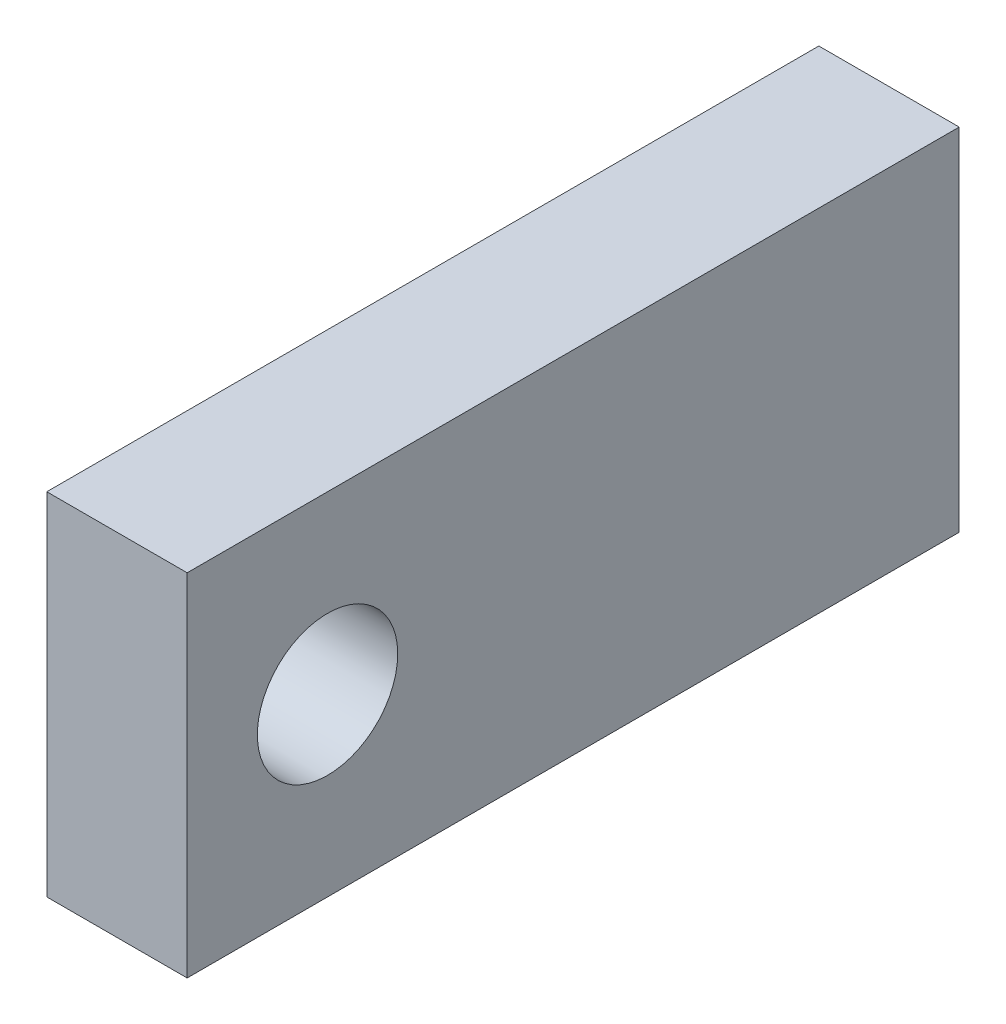
SolidWorks part; units mm, degrees
ref_plane "Front" through (0, 0, 0) normal (0, 0, 1) x (1, 0, 0)
ref_plane "Top" through (0, 0, 0) normal (0, 1, 0) x (1, 0, 0)
ref_plane "Right" through (0, 0, 0) normal (1, 0, 0) x (0, 0, -1)
sketch "Sketch1" plane through (0, 0, 0) normal (0, 0, 1) x (1, 0, 0)
  line L0 (0, -15.875) -> (0, 15.875) construction
  line L1 (-6.35, -15.875) -> (6.35, -15.875)
  line L2 (-6.35, -15.875) -> (-6.35, 15.875)
  line L3 (-6.35, 15.875) -> (6.35, 15.875)
  line L4 (6.35, -15.875) -> (6.35, 15.875)
  line L5 (-6.35, -15.875) -> (6.35, 15.875) construction
  line L6 (-6.35, 15.875) -> (6.35, -15.875) construction
  circle A0 centre (0, 9.525) radius 3.175
  circle A1 centre (0, -9.525) radius 3.175
  point P0 (0, 0)
  dimension "D5" = 6.35
  dimension "D1" = 12.7
  dimension "D2" = 19.05
  dimension "D3" = 6.35
  dimension "D4" = 6.35
extrude "Boss-Extrude1" add sketch "Sketch1" along normal blind 69.85
sketch "Sketch2" plane through (0, 0, 69.85) normal (0, 0, 1) x (1, 0, 0)
  circle A0 centre (0, -9.525) radius 3.175 construction
  circle A1 centre (0, 9.525) radius 3.175 construction
  circle A2 centre (0, -9.525) radius 3.175
  circle A3 centre (0, 9.525) radius 3.175
extrude "Boss-Extrude2" add sketch "Sketch2" against normal offset from surface (50.8 mm away) 19.05 up to face at (3.175, 9.525, 0)
sketch "Sketch3" plane through (6.35, 0, 0) normal (1, 0, 0) x (0, 0, -1)
  line L0 (-57.15, 15.875) -> (-57.15, -15.875) construction
  line L1 (-69.85, 15.875) -> (0, 15.875) construction
  line L2 (-69.85, -15.875) -> (0, -15.875) construction
  line L3 (-69.85, -15.875) -> (-69.85, 15.875) construction
  circle A0 centre (-57.15, 0) radius 6.35
  dimension "D1" = 12.7
  dimension "D2" = 12.7
extrude "Cut-Extrude1" cut sketch "Sketch3" against normal through all
equation "\"D4@Sketch1\"=\"D3@Sketch1\""
